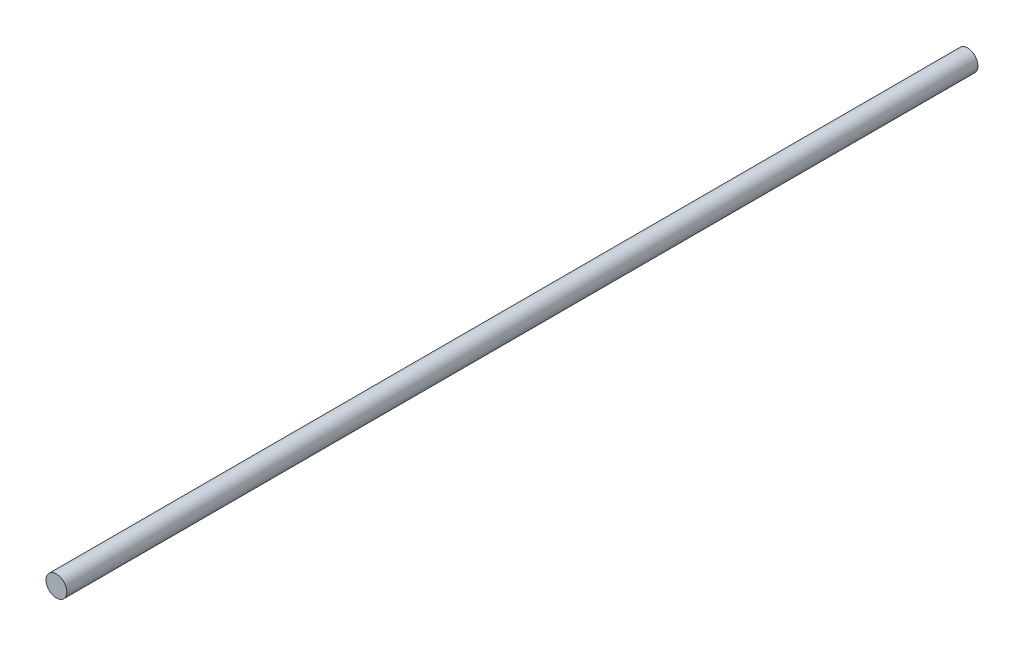
SolidWorks part; units mm, degrees
ref_plane "Plano frontal" through (0, 0, 0) normal (0, 0, 1) x (1, 0, 0)
ref_plane "Plano superior" through (0, 0, 0) normal (0, 1, 0) x (1, 0, 0)
ref_plane "Plano direito" through (0, 0, 0) normal (1, 0, 0) x (0, 0, -1)
sketch "Esboço1" plane through (0, 0, 0) normal (0, 0, 1) x (1, 0, 0)
  circle A0 centre (0, 0) radius 4
  dimension "D1" = 8
extrude "Ressalto-extrusão1" add sketch "Esboço1" along normal blind 350
